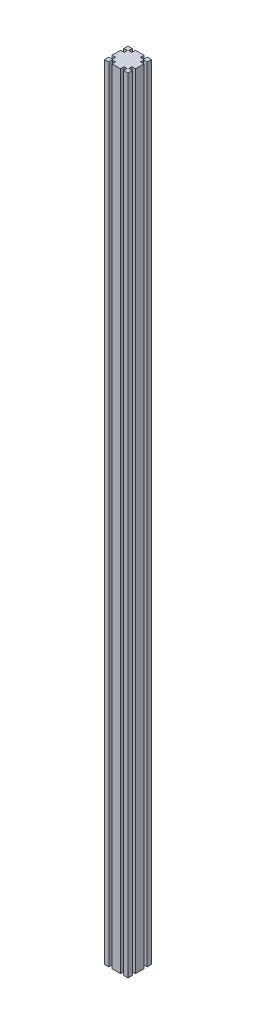
SolidWorks part; units mm, degrees
ref_plane "前视基准面" through (0, 0, 0) normal (0, 0, 1) x (1, 0, 0)
ref_plane "上视基准面" through (0, 0, 0) normal (0, 1, 0) x (1, 0, 0)
ref_plane "右视基准面" through (0, 0, 0) normal (1, 0, 0) x (0, 0, -1)
sketch "草图1" plane through (0, 0, 0) normal (0, 1, 0) x (1, 0, 0)
  line L0 (0, 60) -> (10.9, 60)
  line L1 (0, 0) -> (60, 0)
  line L2 (0, 0) -> (0, 60)
  line L3 (0, 60) -> (60, 60)
  line L4 (60, 0) -> (60, 60)
  line L5 (0, 60) -> (0, 49.1)
  line L6 (0, 49.1) -> (9.2, 49.1)
  line L7 (10.9, 60) -> (10.9, 50.8)
  line L8 (10.9, 50.8) -> (19.1, 50.8)
  line L9 (19.1, 50.8) -> (19.1, 60)
  line L10 (60, 60) -> (49.1, 60)
  line L11 (49.1, 60) -> (49.1, 50.8)
  line L12 (49.1, 50.8) -> (40.9, 50.8)
  line L13 (40.9, 50.8) -> (40.9, 60)
  line L14 (9.2, 49.1) -> (9.2, 40.9)
  line L15 (9.2, 40.9) -> (0, 40.9)
  line L16 (30, 30) -> (30, 60)
  line L17 (30, 60) -> (30, 0)
  line L18 (30, 0) -> (0, 30)
  line L19 (0, 30) -> (30, 30)
  line L20 (60, 30) -> (30, 30)
  line L21 (49.1, 0) -> (49.1, 9.2)
  line L22 (40.9, 9.2) -> (40.9, 0)
  line L23 (49.1, 9.2) -> (40.9, 9.2)
  line L24 (19.1, 9.2) -> (19.1, 0)
  line L25 (10.9, 0) -> (10.9, 9.2)
  line L26 (10.9, 9.2) -> (19.1, 9.2)
  line L27 (0, 10.9) -> (9.2, 10.9)
  line L28 (9.2, 10.9) -> (9.2, 19.1)
  line L29 (9.2, 19.1) -> (0, 19.1)
  line L30 (60, 10.9) -> (50.8, 10.9)
  line L31 (50.8, 10.9) -> (50.8, 19.1)
  line L32 (50.8, 19.1) -> (60, 19.1)
  line L33 (60, 49.1) -> (50.8, 49.1)
  line L34 (50.8, 49.1) -> (50.8, 40.9)
  line L35 (50.8, 40.9) -> (60, 40.9)
  point P4 (30, 30)
extrude "凸台-拉伸1" add sketch "草图1" along normal blind 2000 contours L2 L19 L16 L3 L9 L8 L7 L0 L6 L14 L15 | L35 L34 L33 L4 L3 L11 L12 L13 L16 L20 | L31 L32 L4 L20 L17 L1 L22 L23 L21 L30 | L19 L18 L17 | L29 L28 L27 L2 L1 L25 L26 L24 L18
